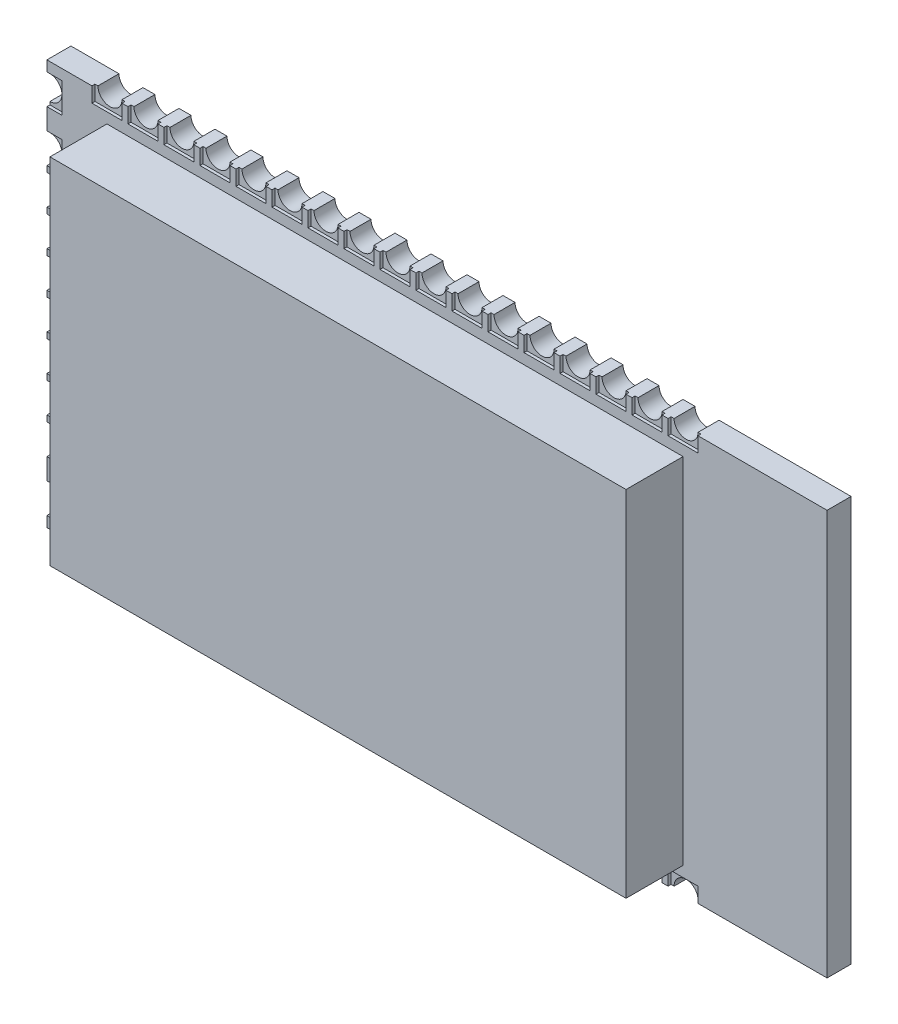
SolidWorks part; units mm, degrees
ref_plane "Front Plane" through (0, 0, 0) normal (0, 0, 1) x (1, 0, 0)
ref_plane "Top Plane" through (0, 0, 0) normal (0, 1, 0) x (1, 0, 0)
ref_plane "Right Plane" through (0, 0, 0) normal (1, 0, 0) x (0, 0, -1)
sketch "Sketch1" plane through (0, 0, 0) normal (0, 0, 1) x (1, 0, 0)
  line L1 (0, 0) -> (26, 0)
  line L2 (0, 0) -> (0, 13.5)
  line L3 (0, 13.5) -> (26, 13.5)
  line L4 (26, 0) -> (26, 13.5)
  dimension "D1" = 26
  dimension "D2" = 13.5
extrude "Boss-Extrude1" add sketch "Sketch1" along normal blind 0.8
sketch "Sketch2" plane through (0, 0, 0.8) normal (0, 0, 1) x (1, 0, 0)
  line L0 (0, 13.5) -> (0, 0) construction
  line L1 (2, 0.85) -> (21.2, 0.85)
  line L2 (2, 0.85) -> (2, 12.65)
  line L3 (2, 12.65) -> (21.2, 12.65)
  line L4 (21.2, 0.85) -> (21.2, 12.65)
  line L5 (0, 0) -> (26, 0) construction
  dimension "D1" = 2
  dimension "D2" = 21.2
  dimension "D3" = 0.85
  dimension "D4" = 12.65
extrude "Boss-Extrude2" add sketch "Sketch2" along normal blind 1.9
ref_plane "Plane1" through (0, 6.75, 0) normal (0, 1, 0) x (1, 0, 0)
sketch "Sketch3" plane through (0, 0, 0.8) normal (0, 0, 1) x (1, 0, 0)
  line L0 (26, 13.5) -> (0, 13.5) construction
  line L1 (1.6, 13.5) -> (2.4, 13.5)
  line L2 (0, 13.5) -> (0, 0) construction
  arc A0 (1.6, 13.5) -> (2.4, 13.5) centre (2, 13.5) ccw
  dimension "D2" = 0.4
  dimension "D1" = 2
extrude "Cut-Extrude1" cut sketch "Sketch3" against normal up to next (0.8 mm away)
sketch "Sketch4" plane through (0, 0, 0.8) normal (0, 0, 1) x (1, 0, 0)
  line L0 (1.6, 13.5) -> (0, 13.5) construction
  line L1 (2.5, 13.5) -> (1.5, 13.5)
  line L2 (2.5, 13.5) -> (2.5, 13)
  line L3 (2.5, 13) -> (1.5, 13)
  line L4 (1.5, 13.5) -> (1.5, 13)
  point P6 (2, 13.5)
  point P7 (2, 13.5)
  dimension "D1" = 1
  dimension "D2" = 0.5
extrude "Cut-Extrude2" cut sketch "Sketch4" against normal blind 0.1
sketch "Sketch5" plane through (0, 0, 0.8) normal (0, 0, 1) x (1, 0, 0)
  line L0 (0, 13.5) -> (0, 0) construction
  line L1 (1.5, 13.5) -> (0, 13.5) construction
  line L2 (0, 13.05) -> (0, 12.25)
  arc A0 (0, 13.05) -> (0, 12.25) centre (0, 12.65) cw
  dimension "D2" = 0.4
  dimension "D1" = 0.85
extrude "Cut-Extrude3" cut sketch "Sketch5" against normal up to next (0.8 mm away)
sketch "Sketch6" plane through (0, 0, 0.8) normal (0, 0, 1) x (1, 0, 0)
  line L0 (0, 13.5) -> (0, 13.05) construction
  line L1 (0, 13.15) -> (0.5, 13.15)
  line L2 (0, 13.15) -> (0, 12.15)
  line L3 (0, 12.15) -> (0.5, 12.15)
  line L4 (0.5, 13.15) -> (0.5, 12.15)
  point P0 (0, 12.65)
  point P8 (0, 12.65)
  dimension "D1" = 1
  dimension "D2" = 0.5
extrude "Cut-Extrude4" cut sketch "Sketch6" against normal blind 0.1
pattern_linear "LPattern1" count 17 spacing 1.2 along (1, 0, 0) of "Cut-Extrude1", "Cut-Extrude2"
mirror "Mirror1" about plane through (0, 6.75, 0) normal (0, 1, 0) of "Cut-Extrude3", "Cut-Extrude4", "LPattern1", "Cut-Extrude1", "Cut-Extrude2"
sketch "Sketch7" plane through (0, 0, 0.8) normal (0, 0, 1) x (1, 0, 0)
  line L0 (0, 12.15) -> (0, 1.35) construction
  line L1 (0, 11.35) -> (0, 10.55)
  arc A0 (0, 11.35) -> (0, 10.55) centre (0, 10.95) cw
  point P5 (0, 12.65)
  dimension "D2" = 0.4
  dimension "D1" = 1.7
extrude "Cut-Extrude5" cut sketch "Sketch7" against normal up to next (0.8 mm away)
sketch "Sketch8" plane through (0, 0, 0.8) normal (0, 0, 1) x (1, 0, 0)
  line L0 (0, 12.15) -> (0, 11.35) construction
  line L1 (0, 11.45) -> (0.5, 11.45)
  line L2 (0, 11.45) -> (0, 10.45)
  line L3 (0, 10.45) -> (0.5, 10.45)
  line L4 (0.5, 11.45) -> (0.5, 10.45)
  point P0 (0, 10.95)
  point P8 (0, 10.95)
  dimension "D1" = 1
  dimension "D2" = 0.5
extrude "Cut-Extrude6" cut sketch "Sketch8" against normal blind 0.1
pattern_linear "LPattern3" count 8 spacing 1.2 along (0, -1, 0) of "Cut-Extrude5", "Cut-Extrude6"
